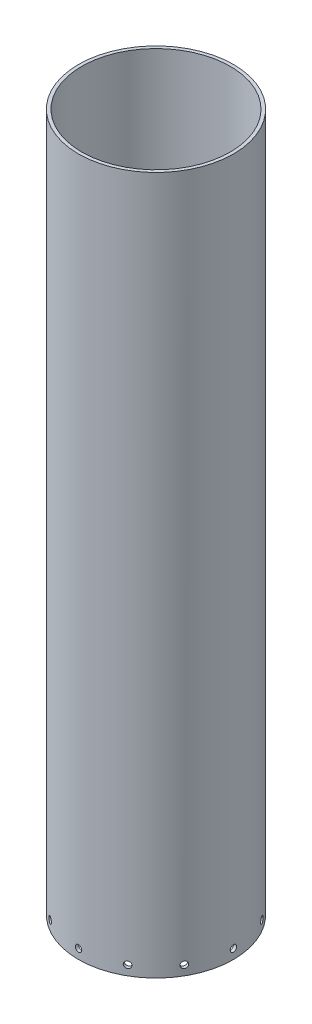
SolidWorks part; units mm, degrees
material "Polycarbonate"
ref_plane "Front Plane" through (0, 0, 0) normal (0, 0, 1) x (1, 0, 0)
ref_plane "Top Plane" through (0, 0, 0) normal (0, 1, 0) x (1, 0, 0)
ref_plane "Right Plane" through (0, 0, 0) normal (1, 0, 0) x (0, 0, -1)
sketch "Sketch2" plane through (0, 0, 0) normal (0, 1, 0) x (1, 0, 0)
  circle A0 centre (0, 0) radius 73.025
  circle A1 centre (0, 0) radius 76.2
  dimension "D1" = 146.05
  dimension "D2" = 152.4
extrude "Boss-Extrude1" add sketch "Sketch2" along normal blind 685.8
sketch "Sketch3" plane through (0, 0, 0) normal (0, 0, 1) x (1, 0, 0)
  line L0 (0, 0) -> (0, 235.745) construction
  line L1 (-76.2, 0) -> (76.2, 0) construction
  circle A0 centre (0, 9.525) radius 3.175
  dimension "D1" = 9.525
  dimension "D2" = 6.35
extrude "Cut-Extrude1" cut sketch "Sketch3" against normal through all
ref_axis "Axis1" through (0, 0, 0) along (0, 1, 0)
pattern_circular "CirPattern1" count 12 over 360 about axis through (0, 0, 0) along (0, 1, 0) of "Cut-Extrude1"
